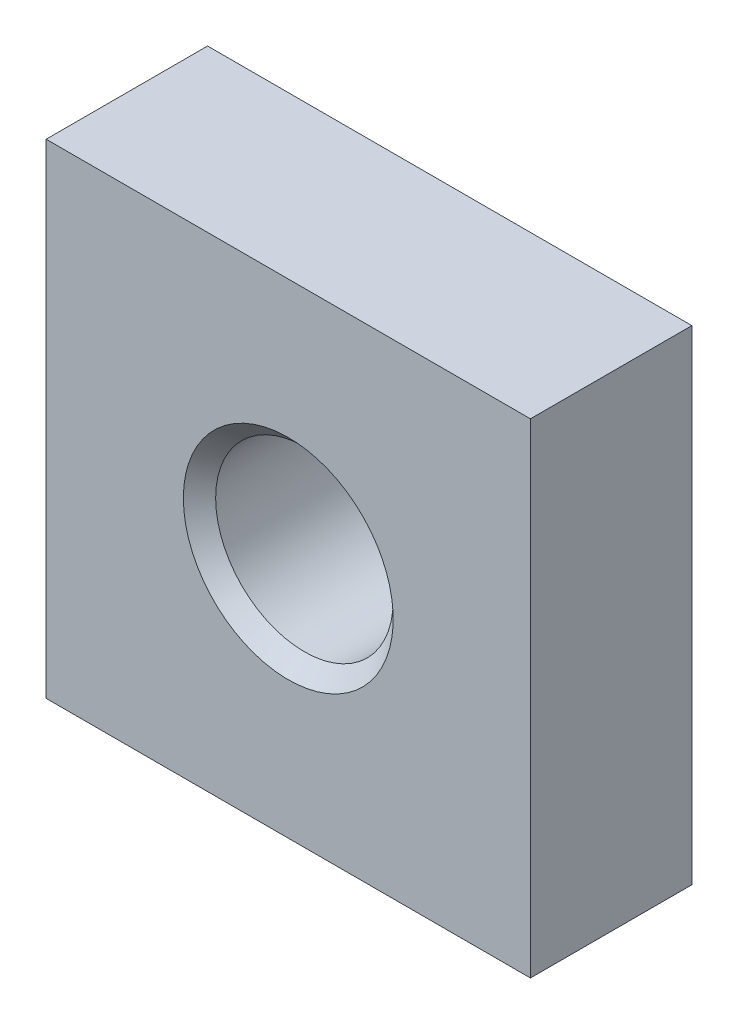
SolidWorks part; units mm, degrees
material "2024-T3"
ref_plane "Спереди" through (0, 0, 0) normal (0, 0, 1) x (1, 0, 0)
ref_plane "Сверху" through (0, 0, 0) normal (0, 1, 0) x (1, 0, 0)
ref_plane "Справа" through (0, 0, 0) normal (1, 0, 0) x (0, 0, -1)
sketch "Эскиз1" plane through (0, 0, 0) normal (0, 0, 1) x (1, 0, 0)
  line L0 (0, 60) -> (60, 0) construction
  line L1 (0, 0) -> (60, 0)
  line L2 (0, 0) -> (0, 60)
  line L3 (0, 60) -> (60, 60)
  line L4 (60, 0) -> (60, 60)
  circle A0 centre (30, 30) radius 11
  dimension "D2" = 22
  dimension "D1" = 60
extrude "Бобышка-Вытянуть1" add sketch "Эскиз1" against normal blind 20
chamfer "Фаска1" distance 2 angle 45 2 edges at (41, 30, 0) (41, 30, -20)
